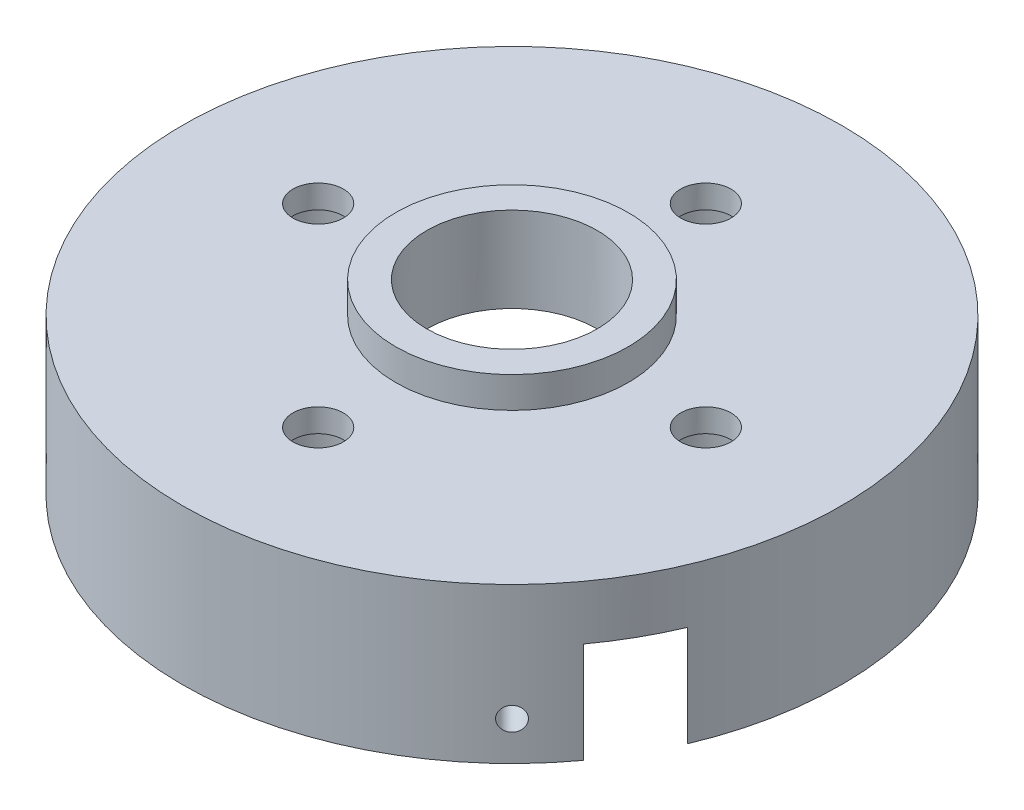
SolidWorks part; units mm, degrees
ref_plane "正面" through (0, 0, 0) normal (0, 0, 1) x (1, 0, 0)
ref_plane "平面" through (0, 0, 0) normal (0, 1, 0) x (1, 0, 0)
ref_plane "右側面" through (0, 0, 0) normal (1, 0, 0) x (0, 0, -1)
sketch "ｽｹｯﾁ1" plane through (0, 0, 0) normal (0, 1, 0) x (1, 0, 0)
  circle A0 centre (0, 0) radius 42.5
  dimension "D1" = 85
extrude "ﾎﾞｽ - 押し出し1" add sketch "ｽｹｯﾁ1" along normal blind 20
sketch "ｽｹｯﾁ2" plane through (0, 20, 0) normal (0, 1, 0) x (1, 0, 0)
  circle A0 centre (0, 0) radius 15
  dimension "D1" = 30
extrude "ﾎﾞｽ - 押し出し2" add sketch "ｽｹｯﾁ2" along normal blind 4
sketch "ｽｹｯﾁ3" plane through (0, 0, 0) normal (0, -1, 0) x (1, 0, 0)
  circle A0 centre (0, 0) radius 38
  dimension "D1" = 76
extrude "ｶｯﾄ - 押し出し1" cut sketch "ｽｹｯﾁ3" against normal blind 13
sketch "ｽｹｯﾁ4" plane through (0, 24, 0) normal (0, 1, 0) x (1, 0, 0)
  circle A0 centre (0, 0) radius 11
  dimension "D1" = 22
extrude "ｶｯﾄ - 押し出し2" cut sketch "ｽｹｯﾁ4" against normal blind 20
sketch "ｽｹｯﾁ5" plane through (0, 20, 0) normal (0, 1, 0) x (1, 0, 0)
  line L0 (0, -25) -> (0, 25) construction
  line L1 (-25, 0) -> (25, 0) construction
  circle A0 centre (0, 0) radius 25 construction
  circle A1 centre (25, 0) radius 3.25
  circle A2 centre (0, -25) radius 3.25
  circle A3 centre (-25, 0) radius 3.25
  circle A4 centre (0, 25) radius 3.25
  point P6 (0, 0)
  point P18 (0, 0)
  dimension "D1" = 50
  dimension "D2" = 6.5
  dimension "D3" = 4
extrude "ｶｯﾄ - 押し出し3" cut sketch "ｽｹｯﾁ5" against normal blind 20
sketch "ｽｹｯﾁ6" plane through (0, 13, 0) normal (0, -1, 0) x (1, 0, 0)
  circle A0 centre (25, 0) radius 6
  circle A1 centre (0, 0) radius 25 construction
  circle A2 centre (0, -25) radius 6
  circle A3 centre (-25, 0) radius 6
  circle A4 centre (0, 25) radius 6
  point P16 (0, 0)
  dimension "D1" = 12
  dimension "D2" = 4
extrude "ｶｯﾄ - 押し出し4" cut sketch "ｽｹｯﾁ6" against normal blind 4
sketch "ｽｹｯﾁ7" plane through (0, 20, 0) normal (0, 1, 0) x (1, 0, 0)
  line L0 (0, -25) -> (25, 0) construction
  line L1 (0, 60.1041) -> (-60.1041, 0) construction
  line L2 (0, 60.1041) -> (60.1041, 0) construction
  line L3 (60.1041, 0) -> (0, -60.1041) construction
  line L4 (-60.1041, 0) -> (0, -60.1041) construction
  line L5 (0, 60.1041) -> (0, -60.1041) construction
  line L6 (60.1041, 0) -> (-60.1041, 0) construction
  circle A0 centre (0, 0) radius 42.5 construction
  point P0 (0, 0)
ref_plane "平面1" through (30.052, 0, 30.052) normal (-0.7071, 0, -0.7071) x (-0.7071, 0, 0.7071)
sketch "ｽｹｯﾁ8" plane through (30.052, 0, 30.052) normal (-0.7071, 0, -0.7071) x (-0.7071, 0, 0.7071)
  line L0 (-42.5, 0) -> (42.5, 0) construction
  line L1 (0, 5) -> (0, 0) construction
  circle A0 centre (0, 5) radius 1.5
  dimension "D1" = 3
  dimension "D2" = 5
extrude "ｶｯﾄ - 押し出し5" cut sketch "ｽｹｯﾁ8" along normal blind 100
ref_plane "平面2" through (-30.052, 0, 30.052) normal (-0.7071, 0, 0.7071) x (0.7071, 0, 0.7071)
sketch "ｽｹｯﾁ9" plane through (-30.052, 0, 30.052) normal (-0.7071, 0, 0.7071) x (0.7071, 0, 0.7071)
  line L0 (0, 0) -> (0, 5) construction
  line L1 (-42.5, 0) -> (42.5, 0) construction
  circle A0 centre (0, 5) radius 1.5
  dimension "D1" = 3
  dimension "D2" = 5
extrude "ｶｯﾄ - 押し出し6" cut sketch "ｽｹｯﾁ9" against normal blind 100
sketch "ｽｹｯﾁ10" plane through (0, 0, 0) normal (0, -1, 0) x (-1, 0, 0)
  line L0 (25.1023, 34.2947) -> (-34.2947, -25.1023)
  line L1 (-34.2947, -25.1023) -> (-41.0122, -18.3848)
  line L2 (-41.0122, -18.3848) -> (18.3848, 41.0122)
  line L3 (18.3848, 41.0122) -> (25.1023, 34.2947)
  line L4 (25, 0) -> (0, 25) construction
  line L5 (30.052, -30.052) -> (-30.052, 30.052) construction
  circle A1 centre (0, 0) radius 42.5 construction
  dimension "D1" = 85
  dimension "D2" = 9.5
  dimension "D3" = 36
extrude "ｶｯﾄ - 押し出し7" cut sketch "ｽｹｯﾁ10" against normal blind 13
